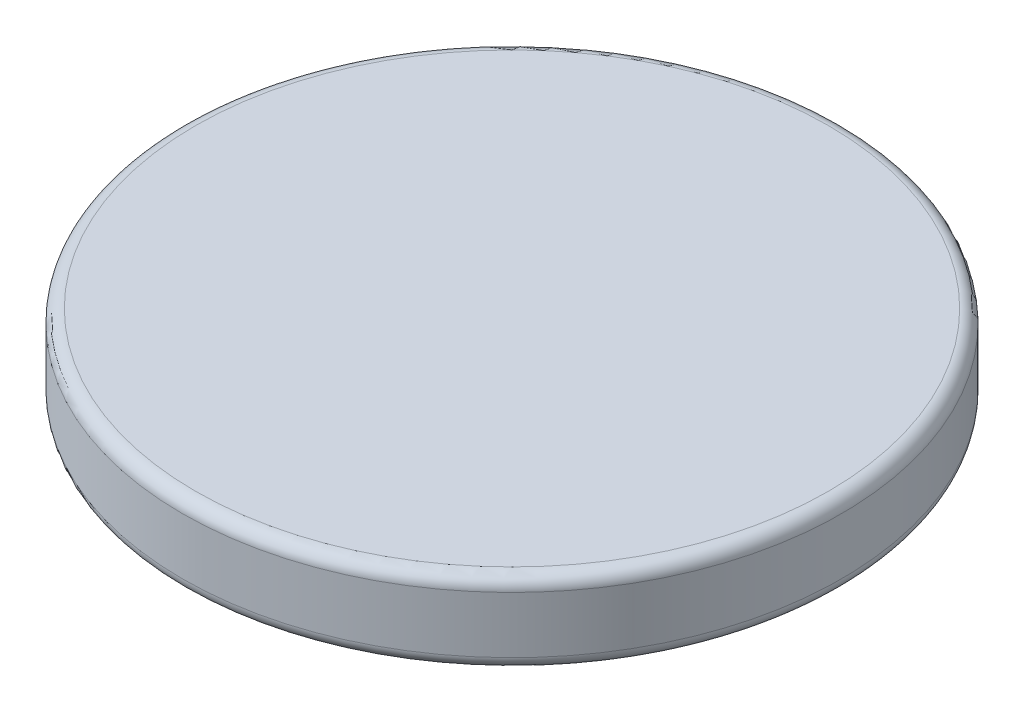
SolidWorks part; units mm, degrees
material "Chrome Stainless Steel"
ref_plane "Front Plane" through (0, 0, 0) normal (0, 0, 1) x (1, 0, 0)
ref_plane "Top Plane" through (0, 0, 0) normal (0, 1, 0) x (1, 0, 0)
ref_plane "Right Plane" through (0, 0, 0) normal (1, 0, 0) x (0, 0, -1)
sketch "Sketch2" plane through (0, 0, 0) normal (0, 1, 0) x (1, 0, 0)
  circle A0 centre (0, 0) radius 6.35
extrude "Boss-Extrude1" add sketch "Sketch2" along normal blind 1.5875
fillet "Fillet1" radius 0.25 2 edges at (0, 0, 6.35) (0, 1.5875, 6.35)
